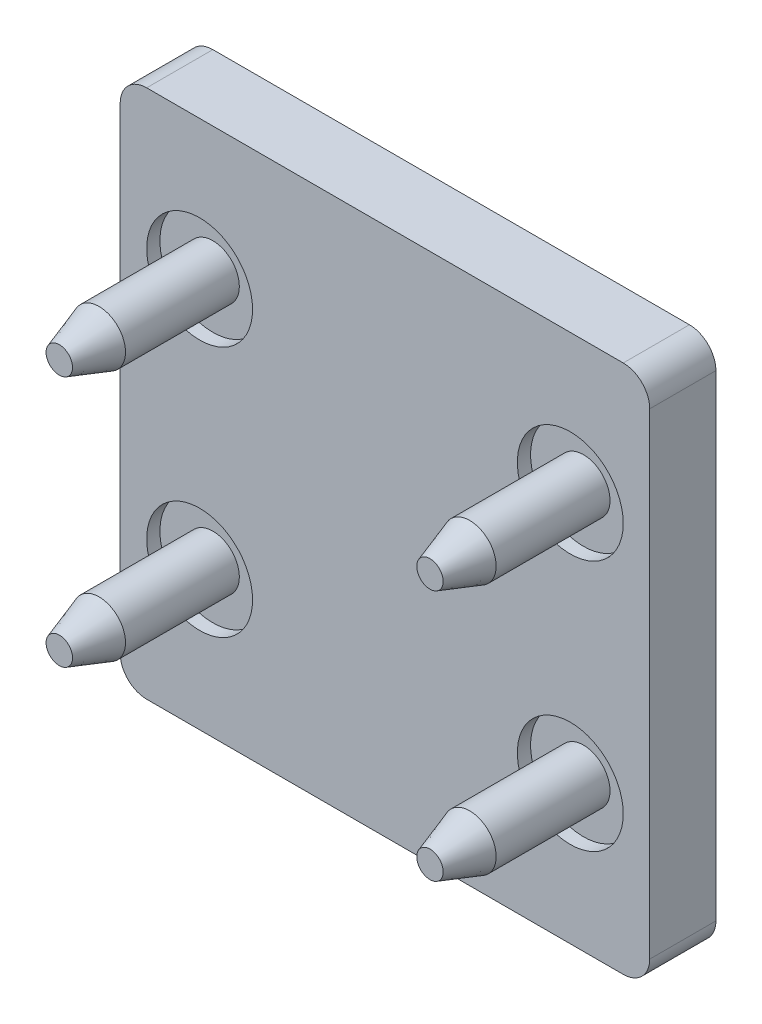
SolidWorks part; units mm, degrees
material "ABS"
ref_plane "Front Plane" through (0, 0, 0) normal (0, 0, 1) x (1, 0, 0)
ref_plane "Top Plane" through (0, 0, 0) normal (0, 1, 0) x (1, 0, 0)
ref_plane "Right Plane" through (0, 0, 0) normal (1, 0, 0) x (0, 0, -1)
ref_plane "Plane1" through (0, 0, 0) normal (0, 0, 1) x (1, 0, 0)
sketch "Sketch1" plane through (0, 0, 0) normal (0, 0, 1) x (1, 0, 0)
  line L0 (-10, 9) -> (-10, -9)
  line L1 (-9, -10) -> (9, -10)
  line L2 (10, -9) -> (10, 9)
  line L3 (9, 10) -> (-9, 10)
  arc A0 (-10, -9) -> (-9, -10) centre (-9, -9) ccw
  arc A1 (9, -10) -> (10, -9) centre (9, -9) ccw
  arc A2 (10, 9) -> (9, 10) centre (9, 9) ccw
  arc A3 (-9, 10) -> (-10, 9) centre (-9, 9) ccw
extrude "Boss-Extrude1" add sketch "Sketch1" against normal blind 2.5
ref_plane "Plane2" through (-7, 0, 0) normal (1, 0, 0) x (0, 0, -1)
sketch "Sketch2" plane through (-7, 0, 0) normal (1, 0, 0) x (0, 0, -1)
  line L0 (0, 4.75) -> (0, 6.75)
  line L1 (0, 6.75) -> (0.5, 6.75)
  line L2 (0.5, 6.75) -> (0.5, 4.75)
  line L3 (0.5, 4.75) -> (0, 4.75)
  line L4 (0.5, 4.75) -> (0, 4.75) construction
revolve "Cut-Revolve1" cut sketch "Sketch2" angle 360 about L4
ref_plane "Plane3" through (7, 0, 0) normal (1, 0, 0) x (0, 0, -1)
sketch "Sketch3" plane through (7, 0, 0) normal (1, 0, 0) x (0, 0, -1)
  line L0 (0, 4.75) -> (0, 6.75)
  line L1 (0, 6.75) -> (0.5, 6.75)
  line L2 (0.5, 6.75) -> (0.5, 4.75)
  line L3 (0.5, 4.75) -> (0, 4.75)
  line L4 (0.5, 4.75) -> (0, 4.75) construction
revolve "Cut-Revolve2" cut sketch "Sketch3" angle 360 about L4
ref_plane "Plane4" through (7, 0, 0) normal (1, 0, 0) x (0, 0, -1)
sketch "Sketch4" plane through (7, 0, 0) normal (1, 0, 0) x (0, 0, -1)
  line L0 (0, -4.75) -> (0, -2.75)
  line L1 (0, -2.75) -> (0.5, -2.75)
  line L2 (0.5, -2.75) -> (0.5, -4.75)
  line L3 (0.5, -4.75) -> (0, -4.75)
  line L4 (0.5, -4.75) -> (0, -4.75) construction
revolve "Cut-Revolve3" cut sketch "Sketch4" angle 360 about L4
ref_plane "Plane5" through (-7, 0, 0) normal (1, 0, 0) x (0, 0, -1)
sketch "Sketch5" plane through (-7, 0, 0) normal (1, 0, 0) x (0, 0, -1)
  line L0 (0, -4.75) -> (0, -2.75)
  line L1 (0, -2.75) -> (0.5, -2.75)
  line L2 (0.5, -2.75) -> (0.5, -4.75)
  line L3 (0.5, -4.75) -> (0, -4.75)
  line L4 (0.5, -4.75) -> (0, -4.75) construction
revolve "Cut-Revolve4" cut sketch "Sketch5" angle 360 about L4
ref_plane "Plane6" through (-7, 0, 0) normal (1, 0, 0) x (0, 0, -1)
sketch "Sketch6" plane through (-7, 0, 0) normal (1, 0, 0) x (0, 0, -1)
  line L0 (-5.3, 4.75) -> (-5.3, 5.25)
  line L1 (-5.3, 5.25) -> (-3.8, 5.75)
  line L2 (-3.8, 5.75) -> (0.5, 5.75)
  line L3 (0.5, 5.75) -> (0.5, 4.75)
  line L4 (0.5, 4.75) -> (-5.3, 4.75)
  line L5 (0.5, 4.75) -> (-5.3, 4.75) construction
revolve "Revolve1" add sketch "Sketch6" angle 360 about L5
ref_plane "Plane7" through (7, 0, 0) normal (1, 0, 0) x (0, 0, -1)
sketch "Sketch7" plane through (7, 0, 0) normal (1, 0, 0) x (0, 0, -1)
  line L0 (-5.3, 4.75) -> (-5.3, 5.25)
  line L1 (-5.3, 5.25) -> (-3.8, 5.75)
  line L2 (-3.8, 5.75) -> (0.5, 5.75)
  line L3 (0.5, 5.75) -> (0.5, 4.75)
  line L4 (0.5, 4.75) -> (-5.3, 4.75)
  line L5 (0.5, 4.75) -> (-5.3, 4.75) construction
revolve "Revolve2" add sketch "Sketch7" angle 360 about L5
ref_plane "Plane8" through (7, 0, 0) normal (1, 0, 0) x (0, 0, -1)
sketch "Sketch8" plane through (7, 0, 0) normal (1, 0, 0) x (0, 0, -1)
  line L0 (-5.3, -4.75) -> (-5.3, -4.25)
  line L1 (-5.3, -4.25) -> (-3.8, -3.75)
  line L2 (-3.8, -3.75) -> (0.5, -3.75)
  line L3 (0.5, -3.75) -> (0.5, -4.75)
  line L4 (0.5, -4.75) -> (-5.3, -4.75)
  line L5 (0.5, -4.75) -> (-5.3, -4.75) construction
revolve "Revolve3" add sketch "Sketch8" angle 360 about L5
ref_plane "Plane9" through (-7, 0, 0) normal (1, 0, 0) x (0, 0, -1)
sketch "Sketch9" plane through (-7, 0, 0) normal (1, 0, 0) x (0, 0, -1)
  line L0 (-5.3, -4.75) -> (-5.3, -4.25)
  line L1 (-5.3, -4.25) -> (-3.8, -3.75)
  line L2 (-3.8, -3.75) -> (0.5, -3.75)
  line L3 (0.5, -3.75) -> (0.5, -4.75)
  line L4 (0.5, -4.75) -> (-5.3, -4.75)
  line L5 (0.5, -4.75) -> (-5.3, -4.75) construction
revolve "Revolve4" add sketch "Sketch9" angle 360 about L5
